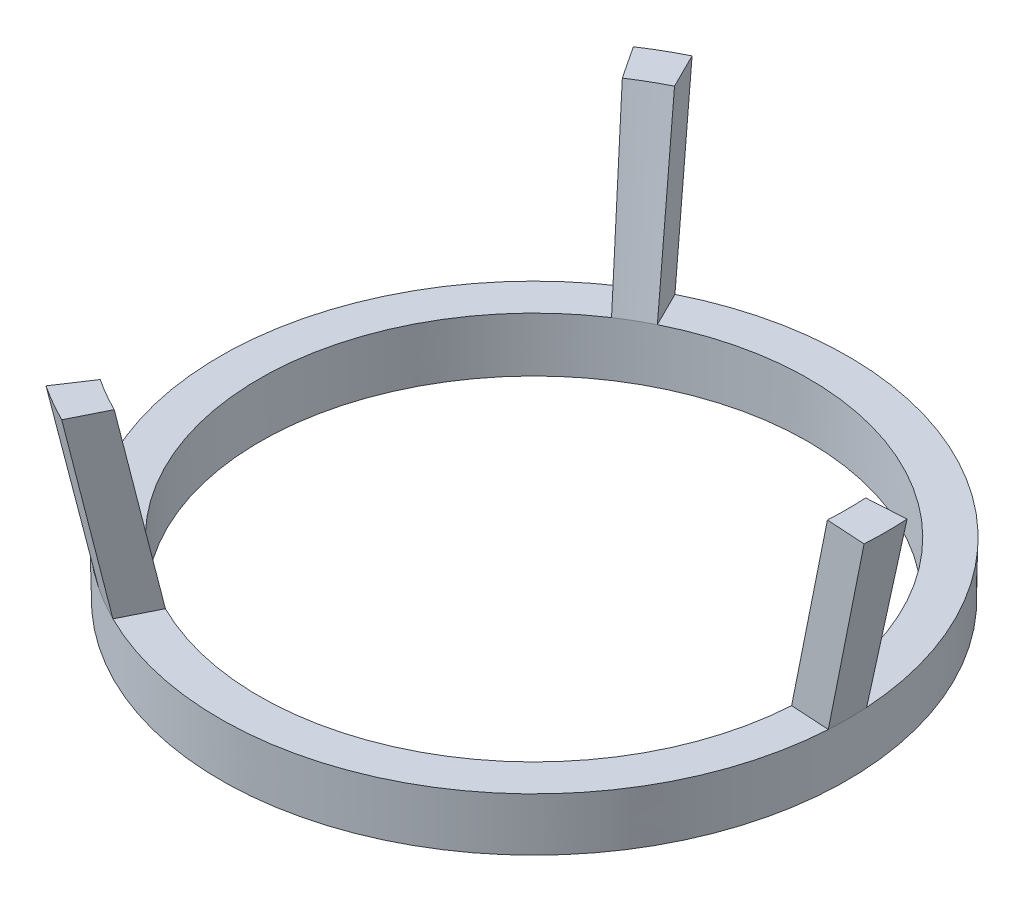
SolidWorks part; units mm, degrees
ref_plane "Front Plane" through (0, 0, 0) normal (0, 0, 1) x (1, 0, 0)
ref_plane "Top Plane" through (0, 0, 0) normal (0, 1, 0) x (1, 0, 0)
ref_plane "Right Plane" through (0, 0, 0) normal (1, 0, 0) x (0, 0, -1)
sketch "Sketch1" plane through (0, 0, 0) normal (0, 0, 1) x (1, 0, 0)
  line L0 (0, 0) -> (0, 16.1217) construction
  line L1 (14, 0) -> (14.0498, 2.75)
  line L2 (14.0498, 2.75) -> (16.0498, 2.75)
  line L3 (16.0498, 2.75) -> (16, 0)
  line L4 (16, 0) -> (14, 0)
  line L5 (16, 0) -> (16.315, 17.4) construction
  point P5 (0, 0)
  point P9 (14, 5.5361)
  point P10 (16.315, 1.3094)
  point P11 (14, 5.2904)
revolve "Revolve1" add sketch "Sketch1" angle 360 about L0
ref_plane "Plane2" through (0, 0.25, 0) normal (0, 1, 0) x (1, 0, 0)
sketch "Sketch2" plane through (0, 0, 0) normal (0, 0, 1) x (1, 0, 0)
  line L0 (14.0498, 2.75) -> (16, 12)
  line L1 (16, 12) -> (18, 12)
  line L2 (18, 12) -> (16.0498, 2.75)
  line L3 (16.0498, 2.75) -> (14.0498, 2.75)
  line L8 (0, 0) -> (0, 2.75) construction
  line L9 (14, 0) -> (14.0498, 2.75) construction
  dimension "D1" = 12
  dimension "D2" = 36
revolve "Revolve2" add sketch "Sketch2" angle 7 mid plane about L8
pattern_circular "CirPattern1" count 3 over 360 about axis through (0, 0, 0) along (0, 1, 0) of "Revolve2"
equation "\"Base Layer Height\" = 0"
equation "\"Layer Thickness\" = .25"
equation "\"D5@Sketch1\"=\"Base Layer Height\"+\"Layer Thickness\"+2.5"
